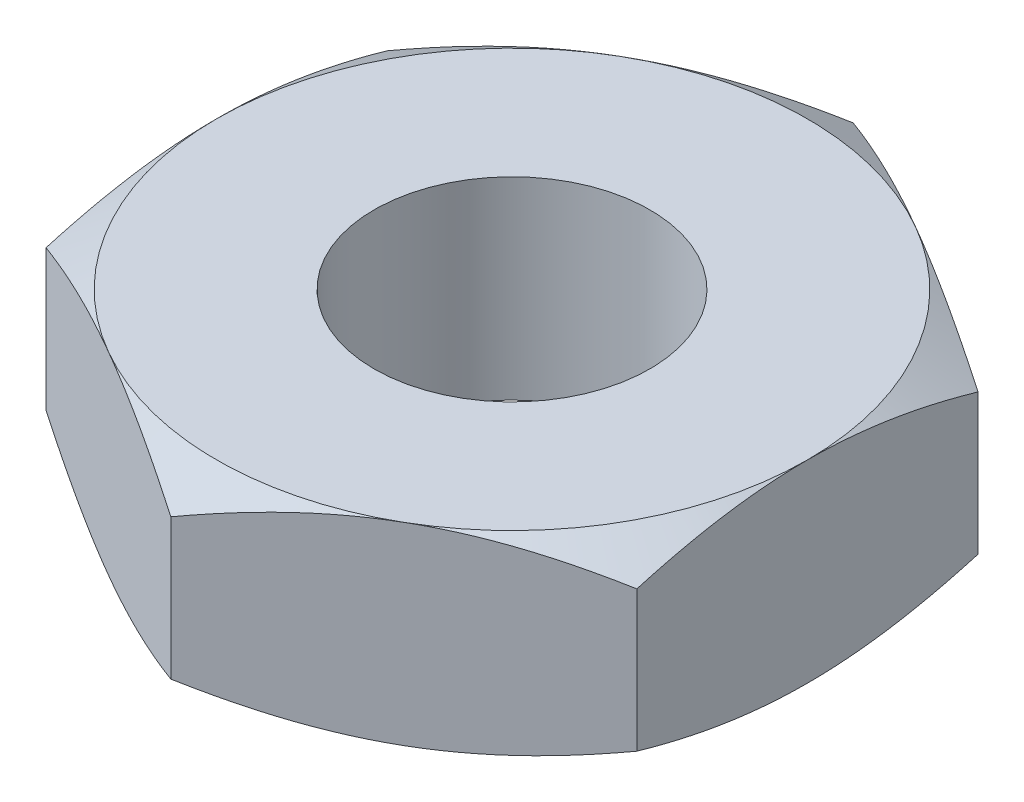
SolidWorks part; units mm, degrees
ref_plane "前视基准面" through (0, 0, 0) normal (0, 0, 1) x (1, 0, 0)
ref_plane "上视基准面" through (0, 0, 0) normal (0, 1, 0) x (1, 0, 0)
ref_plane "右视基准面" through (0, 0, 0) normal (1, 0, 0) x (0, 0, -1)
sketch "草图1" plane through (0, 0, 0) normal (0, 1, 0) x (1, 0, 0)
  line L0 (0, 0) -> (0, 3.1754) construction
  line L1 (0, 3.1754) -> (-2.75, 1.5877)
  line L2 (-2.75, 1.5877) -> (-2.75, -1.5877)
  line L3 (-2.75, -1.5877) -> (0, -3.1754)
  line L4 (0, -3.1754) -> (2.75, -1.5877)
  line L5 (2.75, -1.5877) -> (2.75, 1.5877)
  line L6 (2.75, 1.5877) -> (0, 3.1754)
  circle A0 centre (0, 0) radius 2.75 construction
  dimension "D1" = 5.5
extrude "凸台-拉伸1" add sketch "草图1" along normal blind 1.8
sketch "草图4" plane through (0, 1.8, 0) normal (0, 1, 0) x (1, 0, 0)
  circle A0 centre (0, 0) radius 1.2835
  dimension "D1" = 2.567
extrude "切除-拉伸1" cut sketch "草图4" against normal through all
cosmetic thread "装饰螺纹线1" parameters "D2"=3.134
sketch "草图2" plane through (0, 0, 0) normal (1, 0, 0) x (0, 0, -1)
  line L0 (3.1754, 1.8) -> (3.1754, 1.5544)
  line L1 (3.1754, 1.8) -> (3.1754, 0) construction
  line L2 (3.1754, 1.5544) -> (2.75, 1.8)
  line L3 (1.5877, 1.8) -> (3.1754, 1.8) construction
  line L4 (2.75, 1.8) -> (3.1754, 1.8)
  line L5 (0, 0) -> (0, 2.0082) construction
  line L6 (-1.5877, 0) -> (1.5877, 0) construction
  dimension "D1" = 30
  dimension "D2" = 5.5
revolve "切除-旋转1" cut sketch "草图2" angle 360 about L5
sketch "草图3" plane through (0, 0, 0) normal (1, 0, 0) x (0, 0, -1)
  line L0 (3.1754, 0) -> (3.1754, 0.2456)
  line L1 (3.1754, 1.5544) -> (3.1754, 0) construction
  line L2 (3.1754, 0.2456) -> (2.75, 0)
  line L3 (1.5877, 0) -> (3.1754, 0) construction
  line L4 (2.75, 0) -> (3.1754, 0)
  line L5 (0, 0) -> (0, 2.0879) construction
  dimension "D1" = 30
  dimension "D2" = 5.5
revolve "切除-旋转2" cut sketch "草图3" angle 360 about L5
